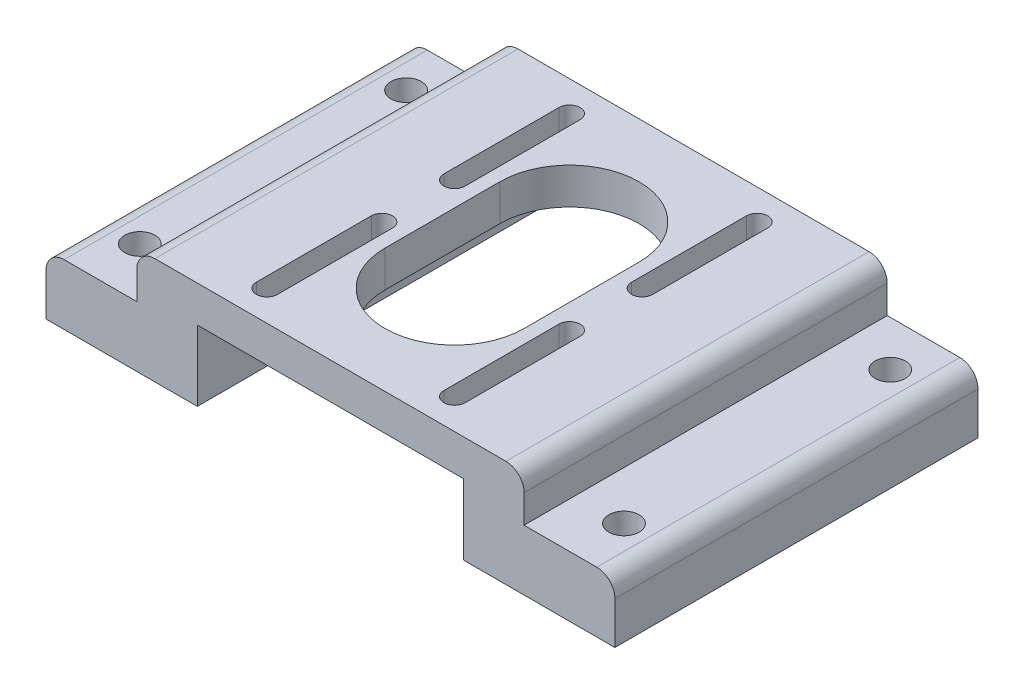
SolidWorks part; units mm, degrees
ref_plane "Front Plane" through (0, 0, 0) normal (0, 0, 1) x (1, 0, 0)
ref_plane "Top Plane" through (0, 0, 0) normal (0, 1, 0) x (1, 0, 0)
ref_plane "Right Plane" through (0, 0, 0) normal (1, 0, 0) x (0, 0, -1)
sketch "Sketch1" plane through (0, 0, 0) normal (0, 0, 1) x (1, 0, 0)
  line L0 (0, 0) -> (25, 0)
  line L1 (25, 0) -> (25, 11.65)
  line L2 (25, 11.65) -> (69, 11.65)
  line L3 (69, 11.65) -> (69, 0)
  line L4 (69, 0) -> (94, 0)
  line L5 (94, 0) -> (94, 10)
  line L6 (94, 10) -> (79, 10)
  line L7 (79, 10) -> (79, 17.65)
  line L8 (79, 17.65) -> (15, 17.65)
  line L9 (15, 17.65) -> (15, 10)
  line L10 (15, 10) -> (0, 10)
  line L11 (0, 10) -> (0, 0)
  dimension "D1" = 44
  dimension "D2" = 11.65
  dimension "D3" = 10
  dimension "D4" = 6
  dimension "D5" = 10
  dimension "D6" = 15
extrude "Boss-Extrude1" add sketch "Sketch1" along normal blind 60
sketch "Sketch2" plane through (0, 17.65, 0) normal (0, 1, 0) x (1, 0, 0)
  line L0 (79, 0) -> (15, 0) construction
  line L1 (79, -60) -> (15, -60) construction
  line L2 (29.75, -36) -> (29.75, -55)
  line L3 (33.25, -36) -> (33.25, -55)
  line L4 (29.75, -24) -> (29.75, -5)
  line L5 (33.25, -5) -> (33.25, -24)
  line L6 (60.75, -5) -> (60.75, -24)
  line L7 (64.25, -5) -> (64.25, -24)
  line L8 (60.75, -36) -> (60.75, -55)
  line L9 (64.25, -36) -> (64.25, -55)
  line L10 (35.5, -20.5) -> (35.5, -39.5)
  line L11 (58.5, -20.5) -> (58.5, -39.5)
  line L12 (15, 0) -> (0, 0) construction
  line L15 (94, 0) -> (79, 0) construction
  arc A0 (33.25, -5) -> (29.75, -5) centre (31.5, -5) ccw
  arc A1 (64.25, -5) -> (60.75, -5) centre (62.5, -5) ccw
  arc A2 (33.25, -36) -> (29.75, -36) centre (31.5, -36) ccw
  arc A3 (64.25, -36) -> (60.75, -36) centre (62.5, -36) ccw
  arc A4 (29.75, -24) -> (33.25, -24) centre (31.5, -24) ccw
  arc A5 (60.75, -24) -> (64.25, -24) centre (62.5, -24) ccw
  arc A6 (29.75, -55) -> (33.25, -55) centre (31.5, -55) ccw
  arc A7 (60.75, -55) -> (64.25, -55) centre (62.5, -55) ccw
  arc A8 (58.5, -20.5) -> (35.5, -20.5) centre (47, -20.5) ccw
  arc A9 (35.5, -39.5) -> (58.5, -39.5) centre (47, -39.5) ccw
  circle A10 centre (7, -7.5) radius 2.5
  circle A11 centre (7, -51.5) radius 2.5
  circle A12 centre (87, -7.5) radius 2.5
  circle A13 centre (87, -51.5) radius 2.5
  point P6 (47, 0)
  dimension "D4" = 3.5
  dimension "D2" = 23
  dimension "D14" = 5
  dimension "D15" = 7.5
  dimension "D1" = 31
  dimension "D3" = 31
  dimension "D5" = 5
  dimension "D6" = 31
  dimension "D7" = 15.5
  dimension "D8" = 5
  dimension "D9" = 15.5
  dimension "D10" = 15.5
  dimension "D11" = 44
  dimension "D12" = 44
  dimension "D13" = 80
  dimension "D16" = 7.5
  dimension "D17" = 40
extrude "Cut-Extrude1" cut sketch "Sketch2" against normal through all
fillet "Fillet1" radius 3 4 edges at (0, 10, 30) (94, 10, 30) (79, 17.65, 30) (15, 17.65, 30)
